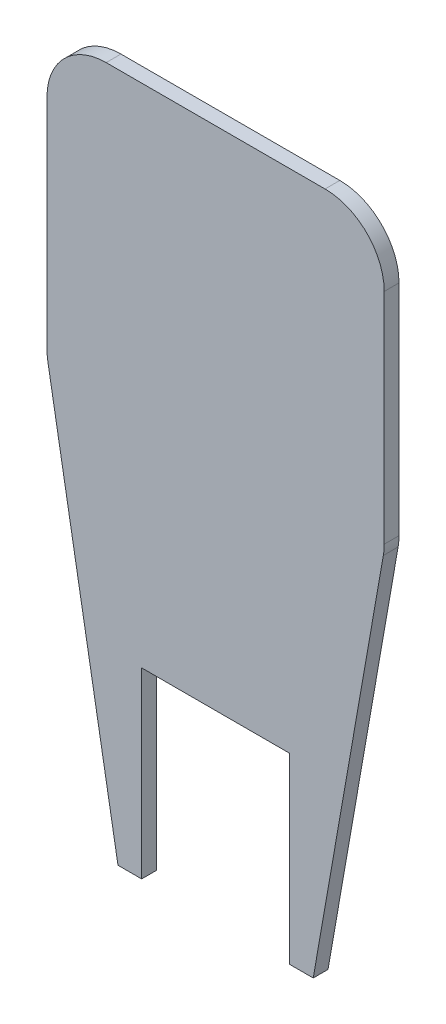
SolidWorks part; units mm, degrees
ref_plane "Alzado" through (0, 0, 0) normal (0, 0, 1) x (1, 0, 0)
ref_plane "Planta" through (0, 0, 0) normal (0, 1, 0) x (1, 0, 0)
ref_plane "Vista lateral" through (0, 0, 0) normal (1, 0, 0) x (0, 0, -1)
sketch "Croquis1" plane through (0, 0, 0) normal (0, 0, 1) x (1, 0, 0)
  line L0 (-16.5, -88) -> (-12.5, -88)
  line L1 (-18.5, 28.5) -> (18.5, 28.5)
  line L2 (-28.5, 18.5) -> (-28.5, -18.5)
  line L4 (28.5, 18.5) -> (28.5, -18.5)
  line L5 (-28.5, 28.5) -> (28.5, -28.5) construction
  line L6 (-28.5, -28.5) -> (28.5, 28.5) construction
  line L7 (12.5, -88) -> (16.5, -88)
  line L8 (-16.5, -88) -> (-28.3506, -20.2223)
  line L9 (28.3506, -20.2223) -> (16.5, -88)
  line L10 (-12.5, -57.1) -> (12.5, -57.1)
  line L11 (-12.5, -57.1) -> (-12.5, -88)
  line L12 (12.5, -57.1) -> (12.5, -88)
  arc A0 (18.5, 28.5) -> (28.5, 18.5) centre (18.5, 18.5) cw
  arc A2 (-28.5, -18.5) -> (-28.3506, -20.2223) centre (-18.5, -18.5) ccw
  arc A3 (-18.5, 28.5) -> (-28.5, 18.5) centre (-18.5, 18.5) ccw
  arc A4 (28.3506, -20.2223) -> (28.5, -18.5) centre (18.5, -18.5) ccw
  point P0 (0, 0)
  point P18 (0, -88)
  point P28 (0, -57.1)
  dimension "D3" = 10
  dimension "D1" = 57
  dimension "D2" = 57
  dimension "D4" = 116.5
  dimension "D5" = 4
  dimension "D6" = 4
  dimension "D8" = 16.5
  dimension "D9" = 30.9
extrude "Saliente-Extruir1" add sketch "Croquis1" along normal blind 2.5
